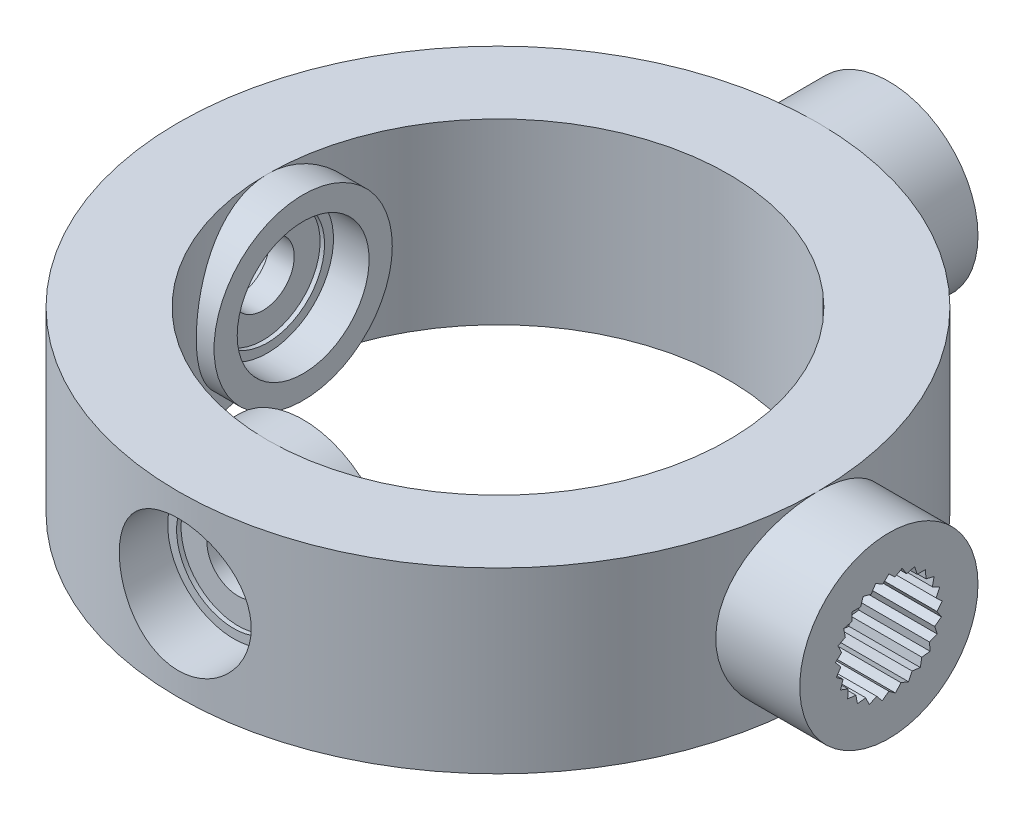
SolidWorks part; units mm, degrees
ref_plane "Front Plane" through (0, 0, 0) normal (0, 0, 1) x (1, 0, 0)
ref_plane "Top Plane" through (0, 0, 0) normal (0, 1, 0) x (1, 0, 0)
ref_plane "Right Plane" through (0, 0, 0) normal (1, 0, 0) x (0, 0, -1)
sketch "Sketch1" plane through (0, 0, 0) normal (0, 1, 0) x (1, 0, 0)
  circle A0 centre (0, 0) radius 17.9289
  dimension "D1" = 35.8579
extrude "Boss-Extrude1" add sketch "Sketch1" along normal blind 10 contours A0
sketch "Sketch2" plane through (0, 10, 0) normal (0, 1, 0) x (1, 0, 0)
  circle A2 centre (0, 0) radius 12.9289
  circle A3 centre (0, 0) radius 12.9289
  dimension "D1" = 5
extrude "Cut-Extrude1" cut sketch "Sketch2" against normal through all
sketch "Sketch3" plane through (0, 0, 0) normal (0, 0, 1) x (1, 0, 0)
  line L0 (0, 0) -> (0, 10) construction
  line L1 (-17.9289, 0) -> (17.9289, 0) construction
  line L2 (12.9289, 10) -> (-12.9289, 10) construction
  line L3 (0, 5) -> (17.9289, 5) construction
  line L4 (17.9289, 0) -> (17.9289, 10) construction
  line L5 (0, 5) -> (-17.9289, 5) construction
  line L6 (-17.9289, 10) -> (-17.9289, 0) construction
  line L7 (17.9289, 5) -> (21.9289, 5) construction
  dimension "D1" = 4
ref_plane "Plane1" through (21.9289, 0, 0) normal (1, 0, 0) x (0, 0, -1)
sketch "Sketch4" plane through (21.9289, 0, 0) normal (1, 0, 0) x (0, 0, -1)
  line L0 (0, 0) -> (0, 10) construction
  line L1 (17.9289, 10) -> (-17.9289, 10) construction
  circle A0 centre (0, 5) radius 5
extrude "Boss-Extrude2" add sketch "Sketch4" against normal up to surface (4.7113 mm away)
ref_plane "Plane2" through (-17.9289, 0, 0) normal (1, 0, 0) x (0, 0, -1)
ref_plane "Plane3" through (-10.9289, 0, 0) normal (1, 0, 0) x (0, 0, -1)
sketch "Sketch7" plane through (-10.9289, 0, 0) normal (1, 0, 0) x (0, 0, -1)
  line L0 (12.9289, 10) -> (-12.9289, 10) construction
  circle A0 centre (0, 5) radius 5
extrude "Boss-Extrude4" add sketch "Sketch7" against normal up to surface (0.994 mm away)
sketch "Sketch8" plane through (-17.9289, 0, 0) normal (1, 0, 0) x (0, 0, -1)
  circle A0 centre (0, 5) radius 1.75
  dimension "D1" = 3.5
extrude "Cut-Extrude3" cut sketch "Sketch8" along normal up to surface (7 mm away) up to face at (-10.9289, 5, -5)
sketch "Sketch10" plane through (0, 0, 0) normal (1, 0, 0) x (0, 0, -1)
  line L0 (0, 0) -> (0, 10) construction
  line L1 (0, 5) -> (-17.9289, 5) construction
  line L2 (-17.9289, 10) -> (-17.9289, 0) construction
  line L3 (0, 5) -> (17.9289, 5) construction
  line L4 (17.9289, 5) -> (21.9289, 5) construction
  circle A0 centre (0, 5) radius 5 construction
  dimension "D1" = 4
ref_plane "Plane4" through (0, 0, -21.9289) normal (0, 0, 1) x (1, 0, 0)
sketch "Sketch11" plane through (0, 0, -21.9289) normal (0, 0, 1) x (1, 0, 0)
  line L0 (17.9289, 10) -> (-17.9289, 10) construction
  circle A0 centre (0, 5) radius 5
extrude "Boss-Extrude5" add sketch "Sketch11" along normal up to surface (4.7113 mm away)
ref_plane "Plane5" through (0, 0, 17.9289) normal (0, 0, 1) x (1, 0, 0)
ref_plane "Plane6" through (0, 0, 10.9289) normal (0, 0, 1) x (1, 0, 0)
sketch "Sketch12" plane through (0, 0, 10.9289) normal (0, 0, 1) x (1, 0, 0)
  line L0 (12.9289, 10) -> (-12.9289, 10) construction
  circle A0 centre (0, 5) radius 5
extrude "Boss-Extrude6" add sketch "Sketch12" along normal up to surface (0.9941 mm away)
sketch "Sketch13" plane through (0, 0, 17.9289) normal (0, 0, 1) x (1, 0, 0)
  circle A0 centre (0, 5) radius 1.75
  dimension "D1" = 3.5
extrude "Cut-Extrude4" cut sketch "Sketch13" against normal up to surface (7 mm away) up to face at (5, 5, 10.9289)
sketch "Sketch14" plane through (0, 0, -21.9289) normal (0, 0, -1) x (-1, 0, 0)
  line L0 (0, 5) -> (0, 8) construction
  line L1 (0, 5) -> (0.376, 7.9763) construction
  line L2 (0, 5) -> (-0.376, 7.9763) construction
  line L3 (0, 8) -> (-0.3384, 7.6786)
  line L4 (0, 8) -> (0.3384, 7.6786)
  line L5 (0.7461, 7.9057) -> (0.3384, 7.6786)
  line L6 (0.7461, 7.9057) -> (0.9939, 7.5102)
  line L7 (1.4453, 7.6289) -> (0.9939, 7.5102)
  line L8 (1.4453, 7.6289) -> (1.5869, 7.1842)
  line L9 (2.0536, 7.1869) -> (1.5869, 7.1842)
  line L10 (2.0536, 7.1869) -> (2.0803, 6.7209)
  line L11 (2.533, 6.6075) -> (2.0803, 6.7209)
  line L12 (2.533, 6.6075) -> (2.4429, 6.1495)
  line L13 (2.8532, 5.9271) -> (2.4429, 6.1495)
  line L14 (2.8532, 5.9271) -> (2.652, 5.5059)
  line L15 (2.9941, 5.1884) -> (2.652, 5.5059)
  line L16 (2.9941, 5.1884) -> (2.6945, 4.8305)
  line L17 (2.9469, 4.4379) -> (2.6945, 4.8305)
  line L18 (2.9469, 4.4379) -> (2.5677, 4.1657)
  line L19 (2.7145, 3.7227) -> (2.5677, 4.1657)
  line L20 (2.7145, 3.7227) -> (2.2796, 3.5534)
  line L21 (2.3115, 3.0877) -> (2.2796, 3.5534)
  line L22 (2.3115, 3.0877) -> (1.8482, 3.0319)
  line L23 (1.7634, 2.5729) -> (1.8482, 3.0319)
  line L24 (1.7634, 2.5729) -> (1.3007, 2.6341)
  line L25 (1.1044, 2.2107) -> (1.3007, 2.6341)
  line L26 (1.1044, 2.2107) -> (0.6714, 2.385)
  line L27 (0.376, 2.0237) -> (0.6714, 2.385)
  line L28 (0.376, 2.0237) -> (0, 2.3002)
  line L29 (-0.376, 2.0237) -> (0, 2.3002)
  line L30 (-0.376, 2.0237) -> (-0.6714, 2.385)
  line L31 (-1.1044, 2.2107) -> (-0.6714, 2.385)
  line L32 (-1.1044, 2.2107) -> (-1.3007, 2.6341)
  line L33 (-1.7634, 2.5729) -> (-1.3007, 2.6341)
  line L34 (-1.7634, 2.5729) -> (-1.8482, 3.0319)
  line L35 (-2.3115, 3.0877) -> (-1.8482, 3.0319)
  line L36 (-2.3115, 3.0877) -> (-2.2796, 3.5534)
  line L37 (-2.7145, 3.7227) -> (-2.2796, 3.5534)
  line L38 (-2.7145, 3.7227) -> (-2.5677, 4.1657)
  line L39 (-2.9469, 4.4379) -> (-2.5677, 4.1657)
  line L40 (-2.9469, 4.4379) -> (-2.6945, 4.8305)
  line L41 (-2.9941, 5.1884) -> (-2.6945, 4.8305)
  line L42 (-2.9941, 5.1884) -> (-2.652, 5.5059)
  line L43 (-2.8532, 5.9271) -> (-2.652, 5.5059)
  line L44 (-2.8532, 5.9271) -> (-2.4429, 6.1495)
  line L45 (-2.533, 6.6075) -> (-2.4429, 6.1495)
  line L46 (-2.533, 6.6075) -> (-2.0803, 6.7209)
  line L47 (-2.0536, 7.1869) -> (-2.0803, 6.7209)
  line L48 (-2.0536, 7.1869) -> (-1.5869, 7.1842)
  line L49 (-1.4453, 7.6289) -> (-1.5869, 7.1842)
  line L50 (-1.4453, 7.6289) -> (-0.9939, 7.5102)
  line L51 (-0.7461, 7.9057) -> (-0.9939, 7.5102)
  line L52 (-0.7461, 7.9057) -> (-0.3384, 7.6786)
  circle A0 centre (0, 5) radius 3 construction
  point P19 (0, 5)
  point P83 (0, 5)
  dimension "D1" = 6
  dimension "D2" = 14.4
  dimension "D3" = 7.2
  dimension "D4" = 53.67
  dimension "D5" = 53.67
  dimension "D6" = 25
extrude "Cut-Extrude5" cut sketch "Sketch14" against normal blind 4
pattern_circular "CirPattern1" count 2 over 270 about axis through (0, 0, 0) along (0, 1, 0) of "Cut-Extrude5"
sketch "Sketch15" plane through (0, 0, 17.9289) normal (0, 0, 1) x (1, 0, 0)
  circle A0 centre (0, 5) radius 3.7
  dimension "D1" = 7.4
extrude "Cut-Extrude6" cut sketch "Sketch15" against normal blind 3.1
sketch "Sketch16" plane through (0, 0, 10.9289) normal (0, 0, 1) x (1, 0, 0)
  circle A0 centre (0, 5) radius 3.7
  dimension "D1" = 7.4
extrude "Cut-Extrude7" cut sketch "Sketch16" along normal blind 2
sketch "Sketch17" plane through (0, 0, 14.8289) normal (0, 0, 1) x (1, 0, 0)
  circle A0 centre (0, 5) radius 3.2
  circle A1 centre (0, 5) radius 3.7 construction
  circle A2 centre (0, 5) radius 3.7
  circle M2 centre (0, 5) radius 1.75
  dimension "D1" = 6.4
extrude "Cut-Extrude8" cut sketch "Sketch17" against normal blind 0.25 contours A0 M2
sketch "Sketch18" plane through (0, 0, 12.9289) normal (0, 0, -1) x (-1, 0, 0)
  circle A0 centre (0, 5) radius 3.2
  circle A1 centre (0, 5) radius 3.7 construction
  circle A2 centre (0, 5) radius 3.7
  circle M3 centre (0, 5) radius 1.75
  dimension "D1" = 6.4
extrude "Cut-Extrude9" cut sketch "Sketch18" against normal blind 0.25 contours A0 M3
pattern_circular "CirPattern2" count 2 over 90 about axis through (0, 10, 0) along (0, 1, 0) of "Cut-Extrude9", "Cut-Extrude8", "Cut-Extrude6", "Cut-Extrude7"
